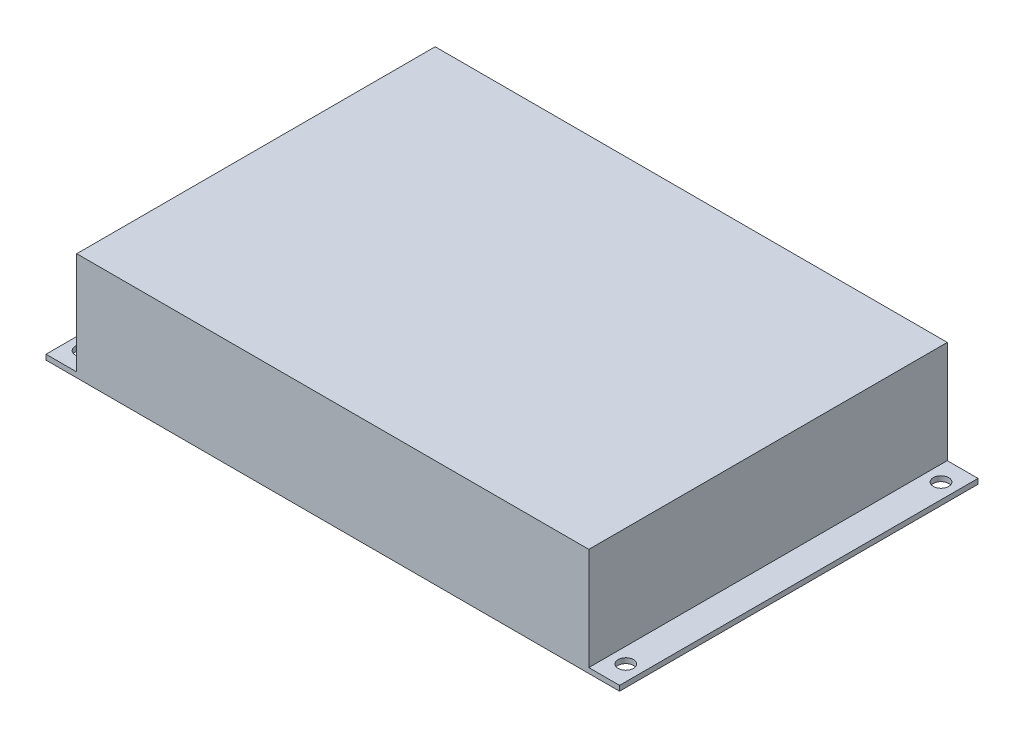
SolidWorks part; units mm, degrees
ref_plane "前视基准面" through (0, 0, 0) normal (0, 0, 1) x (1, 0, 0)
ref_plane "上视基准面" through (0, 0, 0) normal (0, 1, 0) x (1, 0, 0)
ref_plane "右视基准面" through (0, 0, 0) normal (1, 0, 0) x (0, 0, -1)
sketch "草图1" plane through (0, 0, 0) normal (0, 1, 0) x (1, 0, 0)
  line L1 (0, 0) -> (224, 0)
  line L2 (0, 0) -> (0, 140)
  line L3 (0, 140) -> (224, 140)
  line L4 (224, 0) -> (224, 140)
  line L5 (6, 131.55) -> (218, 131.55) construction
  line L6 (6, 131.55) -> (6, 8.45) construction
  line L7 (6, 8.45) -> (218, 8.45) construction
  line L8 (218, 131.55) -> (218, 8.45) construction
  circle A0 centre (6, 131.55) radius 3
  circle A1 centre (218, 131.55) radius 3
  circle A2 centre (218, 8.45) radius 3
  circle A3 centre (6, 8.45) radius 3
  dimension "D7" = 6
  dimension "D1" = 224
  dimension "D2" = 140
  dimension "D3" = 212
  dimension "D4" = 6
  dimension "D5" = 123.1
  dimension "D6" = 8.45
extrude "凸台-拉伸1" add sketch "草图1" along normal blind 2
sketch "草图2" plane through (0, 2, 0) normal (0, 1, 0) x (1, 0, 0)
  line L0 (224, 140) -> (0, 140) construction
  line L1 (12, 140) -> (212, 140)
  line L2 (12, 140) -> (12, 0)
  line L3 (12, 0) -> (212, 0)
  line L4 (212, 140) -> (212, 0)
  line L5 (0, 0) -> (224, 0) construction
  line L6 (0, 140) -> (0, 0) construction
  dimension "D1" = 200
  dimension "D2" = 12
extrude "凸台-拉伸2" add sketch "草图2" along normal blind 40
equation "\"D6@草图1\"=(140-123.1)/2"
